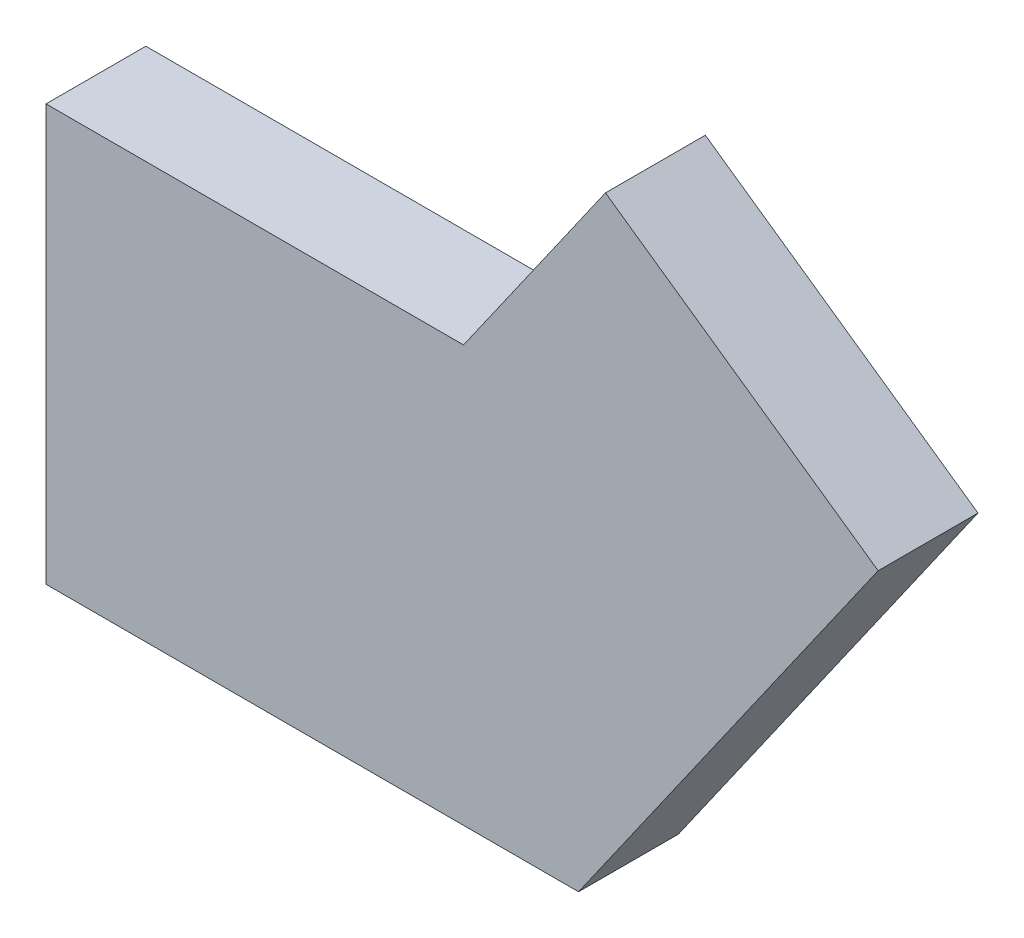
SolidWorks part; units mm, degrees
ref_plane "Front Plane" through (0, 0, 0) normal (0, 0, 1) x (1, 0, 0)
ref_plane "Top Plane" through (0, 0, 0) normal (0, 1, 0) x (1, 0, 0)
ref_plane "Right Plane" through (0, 0, 0) normal (1, 0, 0) x (0, 0, -1)
sketch "Sketch1" plane through (0, 0, 0) normal (0, 0, 1) x (1, 0, 0)
  line L0 (-32, 0) -> (0, 0)
  line L1 (0, 0) -> (18, 25.7067)
  line L2 (18, 25.7067) -> (1.617, 37.1782)
  line L3 (1.617, 37.1782) -> (-6.9103, 25)
  line L4 (-6.9103, 25) -> (-32, 25)
  line L5 (-32, 25) -> (-32, 0)
  dimension "D1" = 50
  dimension "D2" = 25
  dimension "D3" = 125
  dimension "D4" = 32
  dimension "D5" = 20
extrude "Boss-Extrude1" add sketch "Sketch1" along normal mid plane 6
